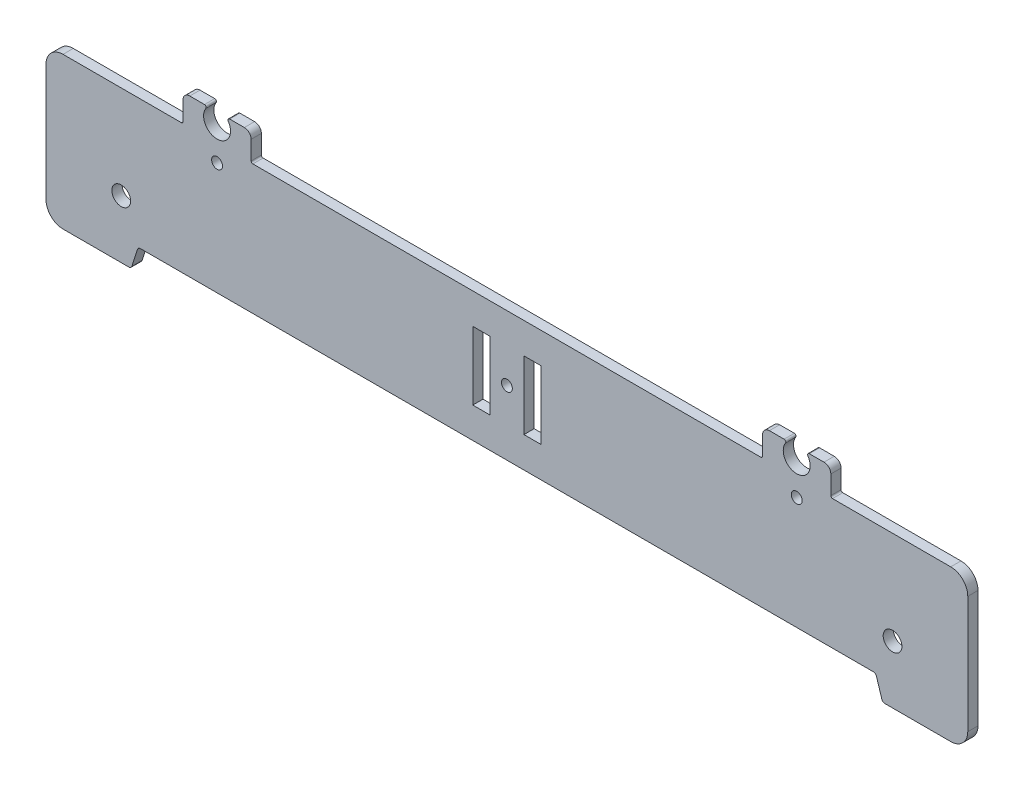
SolidWorks part; units mm, degrees
ref_plane "Alzado" through (0, 0, 0) normal (0, 0, 1) x (1, 0, 0)
ref_plane "Planta" through (0, 0, 0) normal (0, 1, 0) x (1, 0, 0)
ref_plane "Vista lateral" through (0, 0, 0) normal (1, 0, 0) x (0, 0, -1)
sketch "Model" plane through (0, 0, 0) normal (0, 0, 1) x (1, 0, 0)
  line L0 (144.0186, 39.8351) -> (144.0186, 49.8351)
  line L1 (144.0186, 49.8351) -> (149.0186, 49.8351)
  line L2 (149.0186, 49.8351) -> (149.0186, 29.8351)
  line L3 (149.0186, 29.8351) -> (144.0186, 29.8351)
  line L4 (144.0186, 29.8351) -> (144.0186, 39.8351)
  line L5 (154.0186, 58.8363) -> (79.5161, 58.8363)
  line L6 (79.0161, 59.3363) -> (79.0161, 64.8343)
  line L7 (77.0161, 66.8343) -> (72.7, 66.8343)
  line L8 (65.3323, 66.8343) -> (61.0161, 66.8343)
  line L9 (59.0161, 64.8343) -> (59.0161, 59.3363)
  line L10 (58.5161, 58.8363) -> (28.8436, 58.8363)
  line L11 (28.8436, 58.8363) -> (23.8436, 58.8363)
  line L12 (18.8436, 53.8363) -> (18.8436, 19.4487)
  line L13 (23.8436, 14.4487) -> (43.1088, 14.4487)
  line L14 (44.0631, 15.1499) -> (45.6241, 20.1351)
  line L15 (46.5784, 20.8363) -> (154.0186, 20.8339)
  line L16 (154.0186, 58.8363) -> (228.5211, 58.8363)
  line L17 (229.0211, 59.3363) -> (229.0211, 64.8343)
  line L18 (231.0211, 66.8343) -> (235.3373, 66.8343)
  line L19 (242.7049, 66.8343) -> (247.0211, 66.8343)
  line L20 (249.0211, 64.8343) -> (249.0211, 59.3363)
  line L21 (249.5211, 58.8363) -> (279.1936, 58.8363)
  line L22 (279.1936, 58.8363) -> (284.1936, 58.8363)
  line L23 (289.1936, 53.8363) -> (289.1936, 19.4487)
  line L24 (284.1936, 14.4487) -> (264.9284, 14.4487)
  line L25 (263.9741, 15.1499) -> (262.4132, 20.1351)
  line L26 (261.4588, 20.8363) -> (154.0186, 20.8339)
  line L27 (164.0186, 39.8351) -> (164.0186, 49.8351)
  line L28 (164.0186, 49.8351) -> (159.0186, 49.8351)
  line L29 (159.0186, 49.8351) -> (159.0186, 29.8351)
  line L30 (159.0186, 29.8351) -> (164.0186, 29.8351)
  line L31 (164.0186, 29.8351) -> (164.0186, 39.8351)
  circle A0 centre (69.0161, 53.8379) radius 1.6
  circle A1 centre (154.0186, 39.8351) radius 1.6
  circle A2 centre (239.0211, 53.8379) radius 1.6
  circle A3 centre (154.0186, 39.8351) radius 1.6
  circle A4 centre (40.9045, 31.4487) radius 2.75
  circle A5 centre (267.1327, 31.4487) radius 2.75
  arc A6 (79.0161, 59.3363) -> (79.5161, 58.8363) centre (79.5161, 59.3363) ccw
  arc A7 (79.0161, 64.8343) -> (77.0161, 66.8343) centre (77.0161, 64.8343) ccw
  arc A8 (72.7, 66.8343) -> (72.286, 66.0538) centre (72.7, 66.3343) ccw
  arc A9 (65.7462, 66.0538) -> (72.286, 66.0538) centre (69.0161, 63.8379) ccw
  arc A10 (65.7462, 66.0538) -> (65.3323, 66.8343) centre (65.3323, 66.3343) ccw
  arc A11 (61.0161, 66.8343) -> (59.0161, 64.8343) centre (61.0161, 64.8343) ccw
  arc A12 (58.5161, 58.8363) -> (59.0161, 59.3363) centre (58.5161, 59.3363) ccw
  arc A13 (23.8436, 58.8363) -> (18.8436, 53.8363) centre (23.8436, 53.8363) ccw
  arc A14 (18.8436, 19.4487) -> (23.8436, 14.4487) centre (23.8436, 19.4487) ccw
  arc A15 (43.1088, 14.4487) -> (44.0631, 15.1499) centre (43.1088, 15.4487) ccw
  arc A16 (46.5784, 20.8363) -> (45.6241, 20.1351) centre (46.5784, 19.8363) ccw
  arc A17 (228.5211, 58.8363) -> (229.0211, 59.3363) centre (228.5211, 59.3363) ccw
  arc A18 (231.0211, 66.8343) -> (229.0211, 64.8343) centre (231.0211, 64.8343) ccw
  arc A19 (235.7512, 66.0538) -> (235.3373, 66.8343) centre (235.3373, 66.3343) ccw
  arc A20 (235.7512, 66.0538) -> (242.291, 66.0538) centre (239.0211, 63.8379) ccw
  arc A21 (242.7049, 66.8343) -> (242.291, 66.0538) centre (242.7049, 66.3343) ccw
  arc A22 (249.0211, 64.8343) -> (247.0211, 66.8343) centre (247.0211, 64.8343) ccw
  arc A23 (249.0211, 59.3363) -> (249.5211, 58.8363) centre (249.5211, 59.3363) ccw
  arc A24 (289.1936, 53.8363) -> (284.1936, 58.8363) centre (284.1936, 53.8363) ccw
  arc A25 (284.1936, 14.4487) -> (289.1936, 19.4487) centre (284.1936, 19.4487) ccw
  arc A26 (263.9741, 15.1499) -> (264.9284, 14.4487) centre (264.9284, 15.4487) ccw
  arc A27 (262.4132, 20.1351) -> (261.4588, 20.8363) centre (261.4588, 19.8363) ccw
extrude "Saliente-Extruir1" add sketch "Model" along normal blind 3 contours A27 L25 A26 L24 A25 L23 A24 L22 L21 A23 L20 A22 L19 A21 A20 A19 L18 A18 L17 A17 L16 L5 A6 L6 A7 L7 A8 A9 A10 L8 A11 L9 A12 L10 L11 A13 L12 A14 L13 A15 L14 A16 L15 L26 A5 A4 A2
